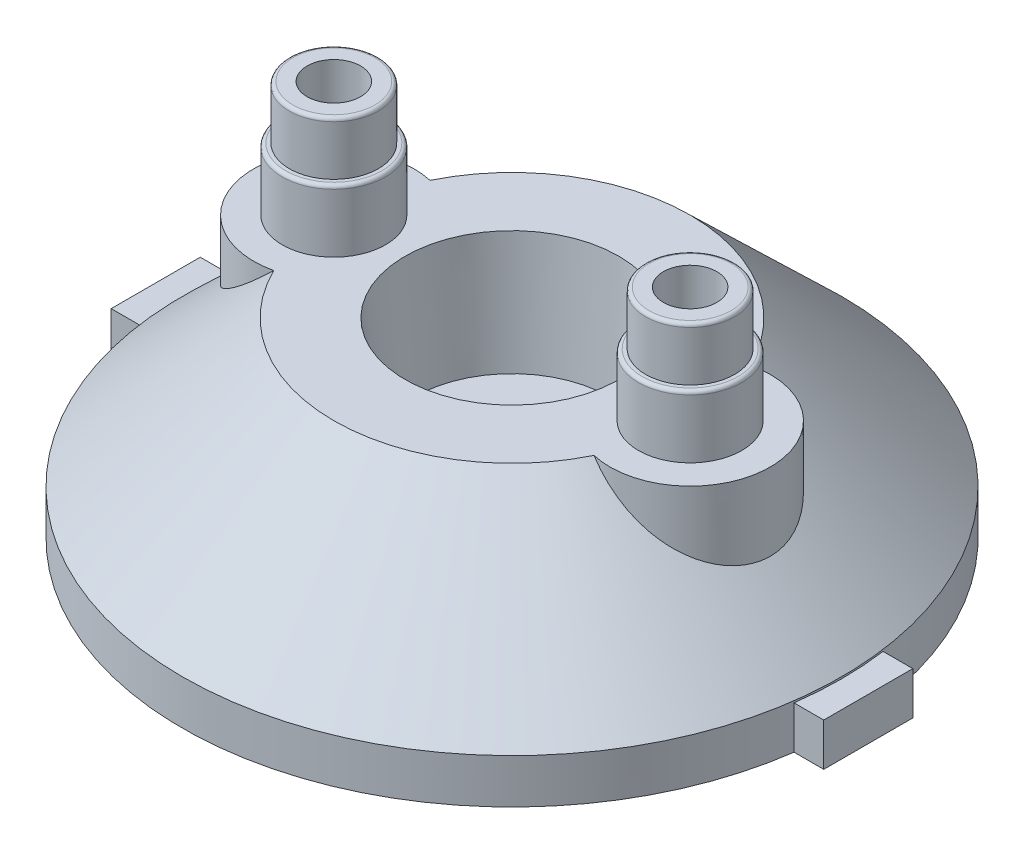
SolidWorks part; units mm, degrees
material "ABS"
ref_plane "Front Plane" through (0, 0, 0) normal (0, 0, 1) x (1, 0, 0)
ref_plane "Top Plane" through (0, 0, 0) normal (0, 1, 0) x (1, 0, 0)
ref_plane "Right Plane" through (0, 0, 0) normal (1, 0, 0) x (0, 0, -1)
sketch "Sketch1" plane through (0, 0, 0) normal (0, 0, 1) x (1, 0, 0)
  line L0 (0, 0) -> (18.5, 0) construction
  line L1 (55, 0) -> (-55, 0) construction
  line L2 (18.5, 0) -> (16.5, 0)
  line L3 (0, 0) -> (6, 0) construction
  line L4 (6, 0) -> (6, 10.7) construction
  line L5 (0, 0) -> (7.5, 0) construction
  line L6 (7.5, 0) -> (7.5, 9) construction
  line L7 (0, 0) -> (7, 0) construction
  line L8 (7, 0) -> (7, 2.6) construction
  line L9 (7.5, 9) -> (7.036, 3.0611)
  line L10 (0, 0) -> (5.5, 0) construction
  line L11 (5.5, 0) -> (5.5, 4.1) construction
  line L12 (5.5, 4.1) -> (6, 10.7)
  line L13 (6.5375, 2.6) -> (2.5, 2.6)
  line L14 (0, -55) -> (0, 55) construction
  line L15 (5.5, 4.1) -> (2.5, 4.1)
  line L16 (2.5, 4.1) -> (2.5, 2.6)
  line L17 (0, 0) -> (0, 2.4395) construction
  line L18 (6, 10.7) -> (10, 10.7)
  line L19 (7.5, 9) -> (9.5, 9)
  line L22 (16.5, 0) -> (16.5, 2)
  line L23 (16.5, 2) -> (9.5, 9)
  line L24 (18.5, 0) -> (18.5, 2.5)
  line L25 (18.5, 2.5) -> (10, 10.7)
  arc A4 (7.036, 3.0611) -> (6.5375, 2.6) centre (6.5375, 3.1) cw
  dimension "D17" = 0.5
  dimension "D1" = 18.5
  dimension "D2" = 2
  dimension "D3" = 6
  dimension "D6" = 7.5
  dimension "D7" = 9
  dimension "D9" = 7
  dimension "D10" = 2.6
  dimension "D11" = 5.5
  dimension "D12" = 4.1
  dimension "D4" = 2.5
  dimension "D13" = 2.5
  dimension "D14" = 10.7
  dimension "D5" = 4
  dimension "D8" = 2
  dimension "D15" = 2
  dimension "D16" = 2.5
revolve "Revolve1" add sketch "Sketch1" angle 360 about L17
ref_plane "Plane1" through (-45, 0, 0) normal (1, 0, 0) x (0, 0, -1)
ref_plane "Plane2" through (-45, 0, 0) normal (1, 0, 0) x (0, 0, -1)
ref_plane "Plane3" through (0, -0.5, 0) normal (0, 1, 0) x (1, 0, 0)
sketch "Sketch4" plane through (0, -0.5, 0) normal (0, 1, 0) x (1, 0, 0)
  line L0 (0, 0) -> (10.6066, -10.6066) construction
  line L2 (-55, 0) -> (55, 0) construction
  circle A0 centre (10.6066, -10.6066) radius 1.5
  circle A1 centre (10.6066, -10.6066) radius 2.75
  dimension "D2" = 45
  dimension "D3" = 5.5
  dimension "D1" = 15
extrude "Boss-Extrude2" add sketch "Sketch4" along normal blind 3
pattern_circular "CirPattern1" count 4 over 360 about axis through (0, 0, 0) along (0, 1, 0) of "Boss-Extrude2"
sketch "Sketch5" plane through (0, 10.7, 0) normal (0, 1, 0) x (1, 0, 0)
  line L0 (-55, 0) -> (55, 0) construction
  line L1 (0, -55) -> (0, 55) construction
  arc A0 (5.7875, -1.5827) -> (5.7875, 1.5827) centre (10, 0) ccw
  arc A1 (5.7875, -1.5827) -> (5.7875, 1.5827) centre (0, 0) ccw
  arc A2 (-5.7875, -1.5827) -> (-5.7875, 1.5827) centre (0, 0) cw
  arc A3 (-5.7875, -1.5827) -> (-5.7875, 1.5827) centre (-10, 0) cw
  dimension "D1" = 9
  dimension "D2" = 10
  dimension "D4" = 6
  dimension "D3" = 0
extrude "Boss-Extrude6" add sketch "Sketch5" against normal up to body separate body
sketch "Sketch6" plane through (0, 10.7, 0) normal (0, 1, 0) x (1, 0, 0)
  line L0 (0, -55) -> (0, 55) construction
  circle A0 centre (10, 0) radius 2.9
  circle A1 centre (-10, 0) radius 2.9
  dimension "D1" = 5.8
  dimension "D2" = 10
extrude "Boss-Extrude7" add sketch "Sketch6" along normal blind 3.5
sketch "Sketch7" plane through (0, 14.2, 0) normal (0, 1, 0) x (1, 0, 0)
  line L1 (0, -55) -> (0, 55) construction
  circle A0 centre (10, 0) radius 2.5
  circle A1 centre (-10, 0) radius 2.5
  dimension "D1" = 5
  dimension "D2" = 10
extrude "Boss-Extrude8" add sketch "Sketch7" along normal blind 3
fillet "Fillet1" radius 0.2 4 edges at (-10, 17.2, -2.5) (10, 17.2, 2.5) (-10, 14.2, -2.9) (10, 14.2, 2.9)
sketch "Sketch8" plane through (0, 17.2, 0) normal (0, 1, 0) x (1, 0, 0)
  line L0 (0, -55) -> (0, 55) construction
  circle A0 centre (10, 0) radius 1.5
  circle A1 centre (-10, 0) radius 1.5
  dimension "D1" = 3
extrude "Cut-Extrude1" cut sketch "Sketch8" against normal through all
sketch "Sketch9" plane through (0, 2.6, 0) normal (0, -1, 0) x (1, 0, 0)
  circle A0 centre (10, 0) radius 3
  dimension "D1" = 6
extrude "Cut-Extrude2" cut sketch "Sketch9" against normal up to surface (6.4 mm away)
sketch "Sketch10" plane through (0, 0, 0) normal (0, 1, 0) x (1, 0, 0)
  line L0 (-9.735, 0) -> (9.735, 0) construction
  line L1 (17, 2.5) -> (20, 2.5)
  line L2 (17, 2.5) -> (17, -2.5)
  line L3 (17, -2.5) -> (20, -2.5)
  line L4 (20, 2.5) -> (20, -2.5)
  line L5 (17, 2.5) -> (20, -2.5) construction
  line L6 (17, -2.5) -> (20, 2.5) construction
  line L7 (0, -9.735) -> (0, 9.735) construction
  line L8 (-17, -2.5) -> (-20, 2.5) construction
  line L9 (-17, 2.5) -> (-20, -2.5) construction
  line L10 (-20, 2.5) -> (-20, -2.5)
  line L11 (-17, -2.5) -> (-20, -2.5)
  line L12 (-17, 2.5) -> (-17, -2.5)
  line L13 (-17, 2.5) -> (-20, 2.5)
  point P0 (18.5, 0)
  point P14 (-18.5, 0)
  dimension "D1" = 3
  dimension "D2" = 5
  dimension "D3" = 20
extrude "Boss-Extrude10" add sketch "Sketch10" along normal blind 2.4
equation "\"D12@Sketch1\"=\"D14@Sketch1\" - 0.0066"
equation "\"D13@Sketch1\"=\"D4@Sketch1\""
equation "\"D10@Sketch1\"=\"D14@Sketch1\"- 0.0081"
